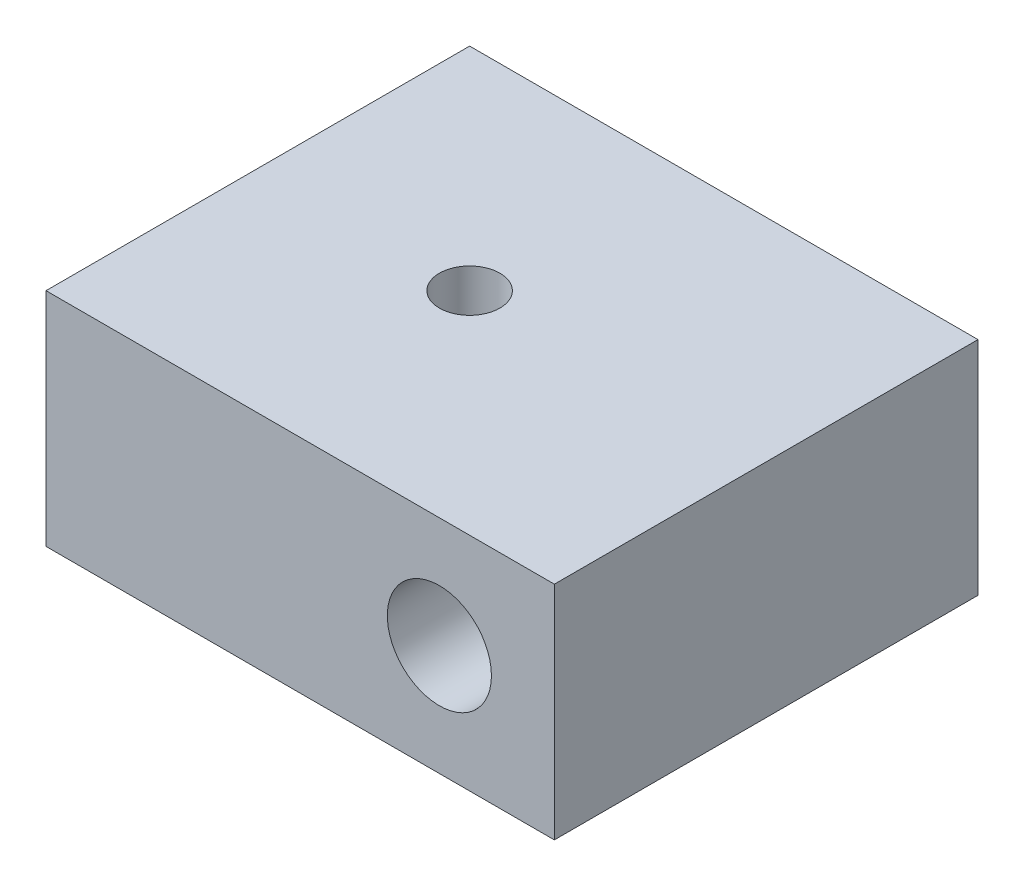
SolidWorks part; units mm, degrees
ref_plane "Front Plane" through (0, 0, 0) normal (0, 0, 1) x (1, 0, 0)
ref_plane "Top Plane" through (0, 0, 0) normal (0, 1, 0) x (1, 0, 0)
ref_plane "Right Plane" through (0, 0, 0) normal (1, 0, 0) x (0, 0, -1)
sketch "Sketch1" plane through (0, 0, 0) normal (0, 1, 0) x (1, 0, 0)
  line L1 (0, 0) -> (42, 0)
  line L2 (0, 0) -> (0, 35)
  line L3 (0, 35) -> (42, 35)
  line L4 (42, 0) -> (42, 35)
  circle A0 centre (17.5, 17.5) radius 2.5
  point P10 (0, 17.5)
  dimension "D2" = 5
  dimension "D1" = 35
  dimension "D3" = 17.5
  dimension "D4" = 42
extrude "Boss-Extrude1" add sketch "Sketch1" along normal blind 18.3
sketch "Sketch2" plane through (0, 0, 0) normal (0, 0, 1) x (1, 0, 0)
  line L1 (17.5, 0) -> (17.5, 18.3) construction
  line L2 (0, 0) -> (42, 0) construction
  line L3 (0, 18.3) -> (42, 18.3) construction
  line L4 (20, 18.3) -> (15, 18.3) construction
  circle A0 centre (32.5, 9.15) radius 4.3
  dimension "D2" = 8.6
  dimension "D1" = 15
  dimension "D3" = 9.15
extrude "Cut-Extrude1" cut sketch "Sketch2" against normal through all
equation "\"8mm hole\" = 8.6mm"
equation "\"22mm hole\"= 23mm"
equation "\"D2@Sketch2\"= \"8mm hole\""
